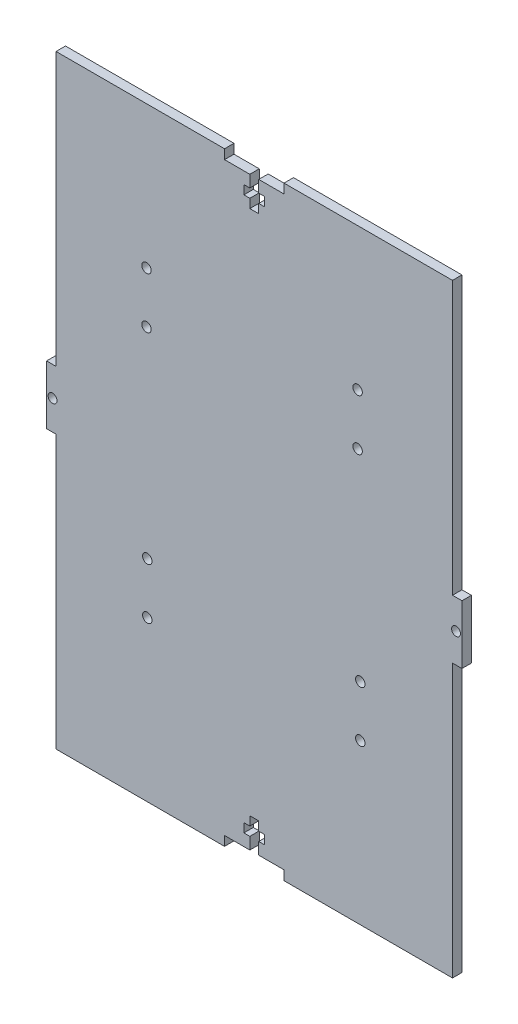
SolidWorks part; units mm, degrees
ref_plane "Front Plane" through (0, 0, 0) normal (0, 0, 1) x (1, 0, 0)
ref_plane "Top Plane" through (0, 0, 0) normal (0, 1, 0) x (1, 0, 0)
ref_plane "Right Plane" through (0, 0, 0) normal (1, 0, 0) x (0, 0, -1)
sketch "Sketch1" plane through (0, 0, 0) normal (0, 0, 1) x (1, 0, 0)
  line L1 (-69.85, 101.6) -> (69.85, 101.6)
  line L2 (-69.85, 101.6) -> (-69.85, -101.6)
  line L3 (-69.85, -101.6) -> (69.85, -101.6)
  line L4 (69.85, 101.6) -> (69.85, -101.6)
  line L5 (-69.85, 101.6) -> (69.85, -101.6) construction
  line L6 (-69.85, -101.6) -> (69.85, 101.6) construction
  point P0 (0, 0)
  dimension "D1" = 203.2
  dimension "D2" = 139.7
extrude "Boss-Extrude1" add sketch "Sketch1" along normal blind 3.18
sketch "Sketch2" plane through (0, 0, 3.18) normal (0, 0, 1) x (1, 0, 0)
  line L0 (0, 0) -> (69.85, 0) construction
  line L1 (-10, 101.6) -> (10, 101.6)
  line L2 (-10, 101.6) -> (-10, 98.42)
  line L3 (-10, 98.42) -> (-1.5, 98.42)
  line L4 (10, 101.6) -> (10, 98.42)
  line L5 (69.85, -101.6) -> (69.85, 101.6) construction
  line L6 (0, 0) -> (0, 101.6) construction
  line L7 (-1.5, 88.42) -> (1.5, 88.42)
  line L8 (-1.5, 88.42) -> (-1.5, 91.42)
  line L10 (1.5, 88.42) -> (1.5, 91.42)
  line L12 (69.85, 101.6) -> (-69.85, 101.6) construction
  line L13 (3.5, 94.42) -> (1.5, 94.42)
  line L14 (3.5, 94.42) -> (3.5, 91.42)
  line L15 (3.5, 91.42) -> (1.5, 91.42)
  line L16 (-3.5, 94.42) -> (-3.5, 91.42)
  line L17 (-10, -101.6) -> (-10, -98.42)
  line L18 (-10, -98.42) -> (-1.5, -98.42)
  line L19 (-1.5, -94.42) -> (-1.5, -98.42)
  line L20 (-1.5, -94.42) -> (-3.5, -94.42)
  line L21 (-3.5, -94.42) -> (-3.5, -91.42)
  line L22 (1.5, 98.42) -> (10, 98.42)
  line L23 (-1.5, 94.42) -> (-3.5, 94.42)
  line L24 (-1.5, -91.42) -> (-3.5, -91.42)
  line L25 (-1.5, -88.42) -> (-1.5, -91.42)
  line L26 (-1.5, -88.42) -> (1.5, -88.42)
  line L27 (-1.5, 91.42) -> (-3.5, 91.42)
  line L28 (1.5, -88.42) -> (1.5, -91.42)
  line L29 (-1.5, 94.42) -> (-1.5, 98.42)
  line L30 (1.5, 94.42) -> (1.5, 98.42)
  line L31 (3.5, -91.42) -> (1.5, -91.42)
  line L32 (3.5, -94.42) -> (3.5, -91.42)
  line L33 (3.5, -94.42) -> (1.5, -94.42)
  line L34 (1.5, -94.42) -> (1.5, -98.42)
  line L35 (1.5, -98.42) -> (10, -98.42)
  line L36 (10, -101.6) -> (10, -98.42)
  line L37 (-10, -101.6) -> (10, -101.6)
  line L38 (-69.85, 101.6) -> (-69.85, -101.6) construction
  line L39 (-69.85, 101.6) -> (-66.67, 101.6)
  line L40 (-69.85, 101.6) -> (-69.85, 9.875)
  line L41 (-69.85, 9.875) -> (-66.67, 9.875)
  line L42 (-66.67, 101.6) -> (-66.67, 9.875)
  line L43 (-69.85, -101.6) -> (-66.67, -101.6)
  line L44 (-69.85, -101.6) -> (-69.85, -9.875)
  line L45 (-69.85, -9.875) -> (-66.67, -9.875)
  line L46 (-66.67, -101.6) -> (-66.67, -9.875)
  line L47 (69.85, -9.875) -> (66.67, -9.875)
  line L48 (66.67, -101.6) -> (66.67, -9.875)
  line L49 (69.85, -101.6) -> (66.67, -101.6)
  line L50 (69.85, -101.6) -> (69.85, -9.875)
  line L51 (69.85, 9.875) -> (66.67, 9.875)
  line L52 (66.67, 101.6) -> (66.67, 9.875)
  line L53 (69.85, 101.6) -> (66.67, 101.6)
  line L54 (69.85, 101.6) -> (69.85, 9.875)
  circle A0 centre (-67.85, 0) radius 1.5
  circle A1 centre (67.85, 0) radius 1.5
  point P0 (0, 50.5662)
  point P5 (0, 32.0079)
  point P10 (15.4931, 34.4893)
  dimension "D11" = 3
  dimension "D12" = 2
  dimension "D1" = 20
  dimension "D2" = 19.75
  dimension "D3" = 4
  dimension "D4" = 3
  dimension "D5" = 3.18
  dimension "D6" = 7
  dimension "D7" = 3
  dimension "D8" = 3
  dimension "D9" = 3.18
  dimension "D10" = 3.18
extrude "Cut-Extrude1" cut sketch "Sketch2" against normal through all
sketch "Sketch3" plane through (0, 0, 0) normal (0, 0, -1) x (-1, 0, 0)
  circle A0 centre (-35.6713, -47.9634) radius 1.59
  circle A1 centre (-35.6713, -30.7773) radius 1.59
extrude "Cut-Extrude2" cut sketch "Sketch3" against normal through all
sketch "Sketch4" plane through (0, 0, 0) normal (0, 0, -1) x (-1, 0, 0)
  circle A0 centre (-34.7507, 53.7803) radius 1.59
  circle A1 centre (-34.7507, 36.5942) radius 1.59
  circle A2 centre (36.2498, 53.7803) radius 1.59
  circle A3 centre (36.2498, 36.5942) radius 1.59
  circle A4 centre (35.9839, -30.7773) radius 1.59
  circle A5 centre (35.9839, -47.9634) radius 1.59
  circle A6 centre (-35.6713, -30.7773) radius 1.59
  circle A7 centre (-35.6713, -47.9634) radius 1.59
extrude "Cut-Extrude3" cut sketch "Sketch4" against normal through all
